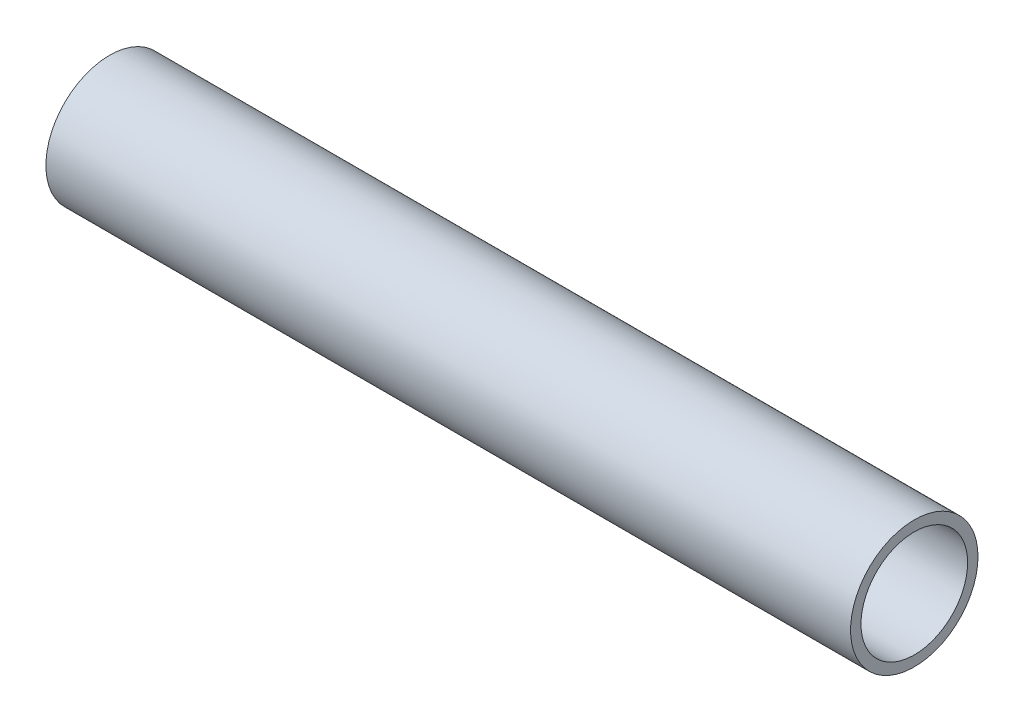
SolidWorks part; units mm, degrees
ref_plane "Front Plane" through (0, 0, 0) normal (0, 0, 1) x (1, 0, 0)
ref_plane "Top Plane" through (0, 0, 0) normal (0, 1, 0) x (1, 0, 0)
ref_plane "Right Plane" through (0, 0, 0) normal (1, 0, 0) x (0, 0, -1)
sketch "Sketch1" plane through (0, 0, 0) normal (1, 0, 0) x (0, 0, -1)
  circle A0 centre (0, 0) radius 24.13
  circle A1 centre (0, 0) radius 20.193
  dimension "D1" = 48.26
  dimension "D2" = 40.386
extrude "Boss-Extrude1" add sketch "Sketch1" along normal blind 304.8
